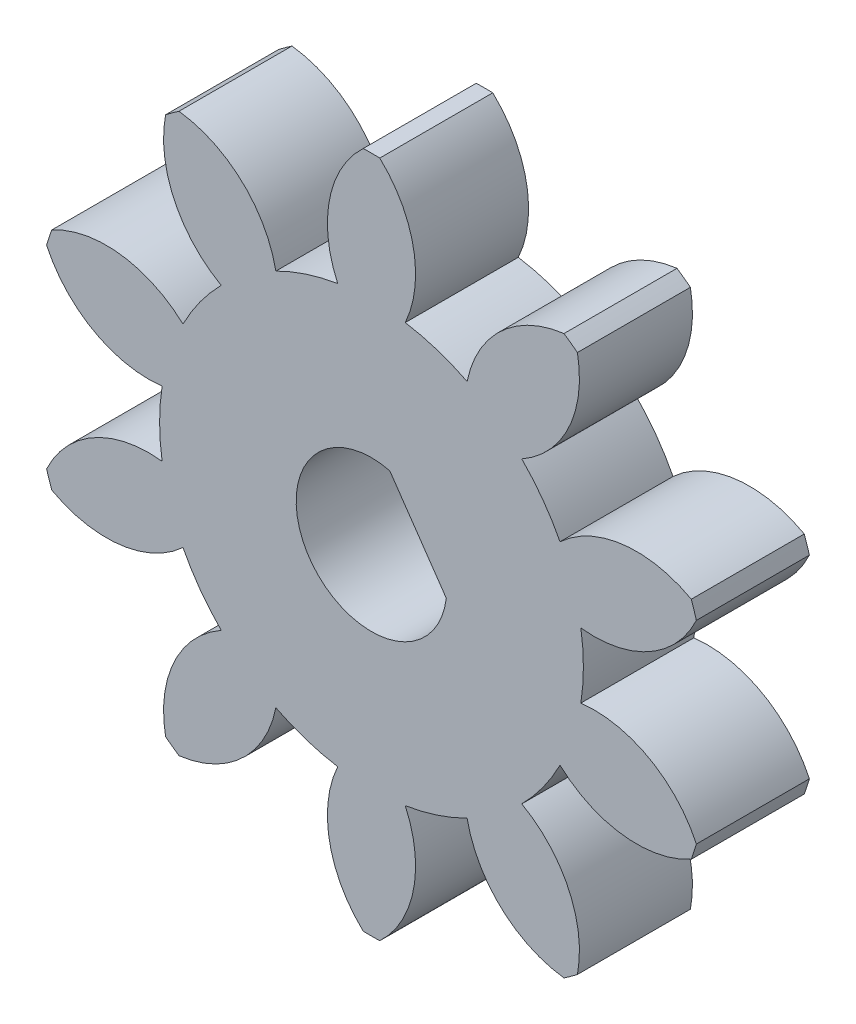
SolidWorks part; units mm, degrees
ref_plane "Front Plane" through (0, 0, 0) normal (0, 0, 1) x (1, 0, 0)
ref_plane "Top Plane" through (0, 0, 0) normal (0, 1, 0) x (1, 0, 0)
ref_plane "Right Plane" through (0, 0, 0) normal (1, 0, 0) x (0, 0, -1)
sketch "Sketch1" plane through (0, 0, 0) normal (0, 0, 1) x (1, 0, 0)
  circle A0 centre (0, 0) radius 9
  dimension "D1" = 18
extrude "Boss-Extrude1" add sketch "Sketch1" along normal blind 3
sketch "Sketch2" plane through (0, 0, 3) normal (0, 0, 1) x (1, 0, 0)
  line L0 (0, 0) -> (0, 30.1085) construction
  line L1 (0, 0) -> (6.8106, 20.9607) construction
  line L5 (3.4639, 6.6522) -> (2.2858, 7.035) construction
  circle A0 centre (0, 0) radius 5.625 construction
  circle A1 centre (0, 0) radius 7.0477 construction
  circle A2 centre (0, 0) radius 7.5 construction
  arc A9 (5.1107, 7.4082) -> (2.5388, 5.0195) centre (5.4805, 4.4311) ccw
  circle A10 centre (0, 0) radius 9 construction
  arc A11 (0.8965, 5.5531) -> (0.2198, 8.9973) centre (-1.8293, 6.8061) ccw
  arc A17 (0.8965, 5.5531) -> (2.5388, 5.0195) centre (0, 0) cw
  arc A18 (0.2198, 8.9973) -> (5.1107, 7.4082) centre (0, 0) cw
  dimension "dedendumDiameter" = 11.25
  dimension "baseDiameter" = 14.0954
  dimension "D1" = 15
  dimension "D3" = 3
  dimension "D2" = 18
  dimension "D4" = 1.1781
extrude "Cut-Extrude1" cut sketch "Sketch2" against normal through all
pattern_circular "CirPattern1" count 10 over 360 about axis through (0, 0, 0) along (0, 0, 1) of "Cut-Extrude1"
sketch "Sketch4" plane through (0, 0, 3) normal (0, 0, 1) x (1, 0, 0)
  line L7 (4.1088, 5.3554) -> (2.1913, 2.8562) construction
  line L8 (5.3212, 4.1529) -> (2.1913, 2.8562)
  line L9 (2.1913, 2.8562) -> (2.6333, 6.2152)
  arc A0 (5.3212, 4.1529) -> (2.6333, 6.2152) centre (0, 0) ccw
  dimension "D1" = 13.5
  dimension "D2" = 60
extrude "Cut-Extrude3" [suppressed] cut sketch "Sketch4" against normal through all
sketch "Sketch5" plane through (0, 0, 3) normal (0, 0, 1) x (1, 0, 0)
  line L0 (1.9856, -0.2397) -> (0.486, 1.94)
  arc A0 (0.486, 1.94) -> (1.9856, -0.2397) centre (0, 0) ccw
  dimension "D1" = 4
  dimension "D2" = 1.5
extrude "Cut-Extrude4" cut sketch "Sketch5" against normal through all
fillet "Fillet1" [suppressed] radius 1.5
pattern_circular "CirPattern2" [suppressed] count 6 over 360
equation "\"module\"= 1.5"
equation "\"teeth\"= 10"
equation "\"pressureAngle\"= 20deg"
equation "\"gearThickness\"= 3"
equation "\"addendumFactor\"= 1"
equation "\"dedendumFactor\"= 1.25"
equation "\"pitch\"= 1 / \"module\""
equation "\"pitchDiameter\"= \"teeth\" / \"pitch\""
equation "\"addendum\"= \"addendumFactor\" / \"pitch\""
equation "\"dedendum\"= \"dedendumFactor\" / \"pitch\""
equation "\"addendumDiameter\"= \"pitchDiameter\" + 2 * \"addendum\""
equation "\"D1@Boss-Extrude1\"=\"gearThickness\""
equation "\"D1@Sketch1\"=\"addendumDiameter\""
equation "\"dedendumDiameter@Sketch2\"=\"pitchDiameter\" - 2 * \"dedendum\""
equation "\"baseDiameter@Sketch2\"=\"pitchDiameter\" * cos ( \"pressureAngle\" )"
equation "\"D1@Sketch2\"=\"pitchDiameter\""
equation "\"D2@Sketch2\"=180/\"teeth\""
equation "\"D1@CirPattern1\"= \"teeth\""
equation "\"D3@Sketch2\"= \"pitchDiameter\"/5"
equation "\"D4@Sketch2\"=PI/2/\"pitch\"/2"
equation "\"D1@Sketch4\"=\"addendumDiameter\"*.75"
equation "\"base\"= \"pitchDiameter\" * cos ( \"pressureAngle\" )"
